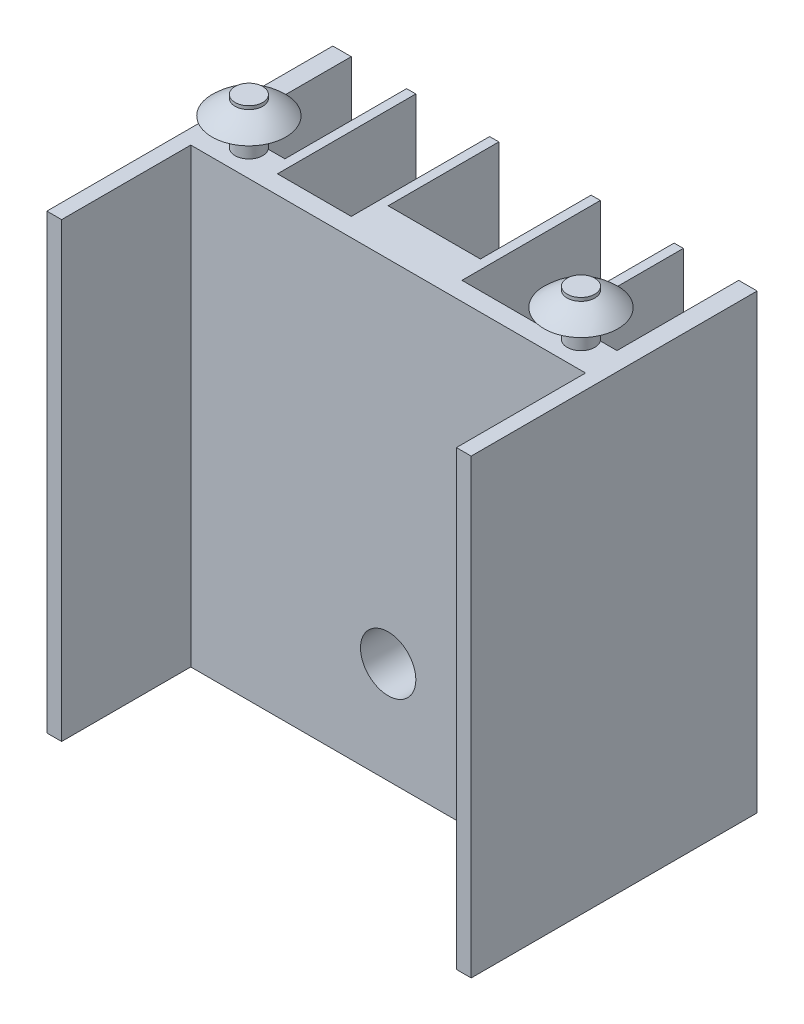
SolidWorks part; units mm, degrees
ref_plane "Ön Düzlem" through (0, 0, 0) normal (0, 0, 1) x (1, 0, 0)
ref_plane "Üst Düzlem" through (0, 0, 0) normal (0, 1, 0) x (1, 0, 0)
ref_plane "Sağ Düzlem" through (0, 0, 0) normal (1, 0, 0) x (0, 0, -1)
sketch "Çizim1" plane through (0, 0, 0) normal (0, 1, 0) x (1, 0, 0)
  line L1 (-11.5, 7.75) -> (11.5, 7.75)
  line L2 (-11.5, 7.75) -> (-11.5, -7.75)
  line L3 (-11.5, -7.75) -> (11.5, -7.75)
  line L4 (11.5, 7.75) -> (11.5, -7.75)
  line L5 (-11.5, 7.75) -> (11.5, -7.75) construction
  line L6 (-11.5, -7.75) -> (11.5, 7.75) construction
  point P0 (0, 0)
  dimension "D1" = 23
  dimension "D2" = 15.5
extrude "Yükseklik-Ekstrüzyon1" add sketch "Çizim1" along normal blind 24.5
sketch "Çizim2" plane through (0, 0, 0) normal (0, 1, 0) x (1, 0, 0)
  line L0 (-11.5, -7.75) -> (11.5, -7.75) construction
  line L1 (-10.7, -7.75) -> (10.7, -7.75)
  line L2 (-10.7, -7.75) -> (-10.7, -0.75)
  line L3 (-10.7, -0.75) -> (10.7, -0.75)
  line L4 (10.7, -7.75) -> (10.7, -0.75)
  line L5 (11.5, -7.75) -> (11.5, 7.75) construction
  line L6 (-11.5, 7.75) -> (-11.5, -7.75) construction
  line L7 (0, 7.75) -> (0, -7.75) construction
  line L9 (11.5, 7.75) -> (-11.5, 7.75) construction
  line L10 (-8.5, 1.1537) -> (-7.5, 1.1537)
  line L11 (2.5, 7.75) -> (-2.5, 7.75)
  line L12 (2.5, 7.75) -> (2.5, 1.75)
  line L13 (2.5, 1.75) -> (-2.5, 1.75)
  line L14 (-2.5, 7.75) -> (-2.5, 1.75)
  line L15 (-7, 7.75) -> (-3, 7.75)
  line L16 (-7, 7.75) -> (-7, 0.25)
  line L17 (-7, 0.25) -> (-3, 0.25)
  line L18 (-3, 7.75) -> (-3, 0.25)
  line L19 (-10.5, 7.75) -> (-7.5, 7.75)
  line L20 (-10.5, 7.75) -> (-10.5, 1.1537)
  line L21 (-10.5, 1.1537) -> (-9.5, 1.1537)
  line L22 (-7.5, 7.75) -> (-7.5, 1.1537)
  line L24 (-9.5, 1.1537) -> (-9.5, 0.25)
  line L25 (-9.5, 0.25) -> (-8.5, 0.25)
  line L26 (-8.5, 1.1537) -> (-8.5, 0.25)
  line L27 (7, 0.25) -> (3, 0.25)
  line L28 (3, 7.75) -> (3, 0.25)
  line L29 (7, 7.75) -> (3, 7.75)
  line L30 (7, 7.75) -> (7, 0.25)
  line L31 (10.5, 7.75) -> (7.5, 7.75)
  line L32 (7.5, 7.75) -> (7.5, 1.1537)
  line L33 (8.5, 1.1537) -> (7.5, 1.1537)
  line L34 (8.5, 1.1537) -> (8.5, 0.25)
  line L35 (9.5, 0.25) -> (8.5, 0.25)
  line L36 (9.5, 1.1537) -> (9.5, 0.25)
  line L37 (10.5, 1.1537) -> (9.5, 1.1537)
  line L38 (10.5, 7.75) -> (10.5, 1.1537)
  dimension "D1" = 0.8
  dimension "D2" = 0.8
  dimension "D3" = 7
  dimension "D4" = 6
  dimension "D5" = 5
  dimension "D6" = 2.5
  dimension "D7" = 4
  dimension "D8" = 0.5
  dimension "D9" = 7.5
  dimension "D10" = 1
  dimension "D11" = 3
  dimension "D12" = 1
  dimension "D13" = 1
extrude "Kes-Ekstrüzyon1" cut sketch "Çizim2" along normal blind 24.5
sketch "Çizim3" plane through (0, 24.5, 0) normal (0, 1, 0) x (1, 0, 0)
  line L0 (0, -0.75) -> (0, 1.75) construction
  line L1 (10.7, -0.75) -> (-10.7, -0.75) construction
  line L2 (-2.5, 1.75) -> (2.5, 1.75) construction
  line L3 (-9, 0.25) -> (-9, 1.1537) construction
  line L4 (-9.5, 0.25) -> (-8.5, 0.25) construction
  circle A2 centre (-9, 0.7018) radius 0.75
  circle A3 centre (9, 0.7018) radius 0.75
  dimension "D1" = 1.5
extrude "Yükseklik-Ekstrüzyon4" add sketch "Çizim3" along normal blind 2.5 and the other way blind 10
ref_plane "Düzlem1" through (-9, 0, 0) normal (-1, 0, 0) x (0, 0, 1)
sketch "Çizim5" plane through (-9, 0, 0) normal (-1, 0, 0) x (0, 0, 1)
  line L0 (-0.7018, 27) -> (-0.7018, 26) construction
  line L1 (0.0482, 27) -> (-1.4518, 27) construction
  line L2 (-0.7018, 26) -> (-2.7018, 26) construction
  line L3 (-2.7018, 26) -> (-0.7018, 26)
  line L4 (-0.7018, 26) -> (-0.7018, 27)
  spline S0 degree 2 poles (-2.7018, 26) (-1.7902, 26.8744) (-0.7018, 27) knots 0 0 0 0.748834 0.748834 0.748834
  dimension "D1" = 1
  dimension "D2" = 2
revolve "Döndür2" add sketch "Çizim5" angle 360 about L4
ref_plane "Düzlem2" through (9, 0, 0) normal (1, 0, 0) x (0, 0, -1)
sketch "Çizim6" plane through (9, 0, 0) normal (1, 0, 0) x (0, 0, -1)
  line L0 (0.7018, 27) -> (0.7018, 26.0104) construction
  line L1 (1.4518, 27) -> (-0.0482, 27) construction
  line L2 (0.7018, 26.0104) -> (-1.2982, 26) construction
  line L3 (-1.2982, 26) -> (0.7018, 26.0104)
  line L4 (0.7018, 26.0104) -> (0.7018, 27)
  spline S0 degree 2 poles (-1.2982, 26) (-0.3866, 26.8744) (0.7018, 27) knots 0 0 0 0.748834 0.748834 0.748834
revolve "Döndür3" add sketch "Çizim6" angle 360 about L4
sketch "Çizim8" plane through (0, 0, 0.75) normal (0, 0, 1) x (1, 0, 0)
  line L0 (0, 0) -> (0, 5.5) construction
  line L1 (10.7, 0) -> (-10.7, 0) construction
  circle A0 centre (0, 5.5) radius 1.5
  dimension "D2" = 3
  dimension "D1" = 5.5
extrude "Kes-Ekstrüzyon3" cut sketch "Çizim8" against normal blind 10
